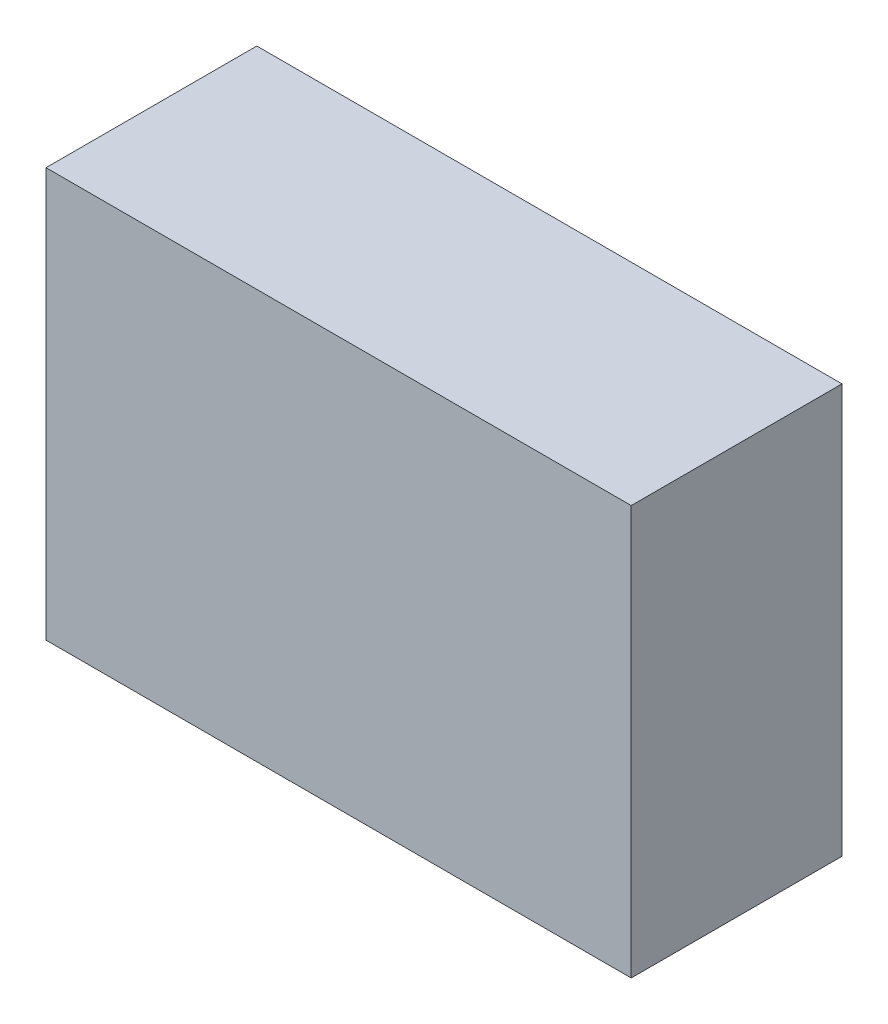
SolidWorks part; units mm, degrees
ref_plane "Front Plane" through (0, 0, 0) normal (0, 0, 1) x (1, 0, 0)
ref_plane "Top Plane" through (0, 0, 0) normal (0, 1, 0) x (1, 0, 0)
ref_plane "Right Plane" through (0, 0, 0) normal (1, 0, 0) x (0, 0, -1)
sketch "Sketch1" plane through (0, 0, 0) normal (0, 0, 1) x (1, 0, 0)
  line L1 (0, 0) -> (59.944, 0)
  line L2 (0, 0) -> (0, 41.91)
  line L3 (0, 41.91) -> (59.944, 41.91)
  line L4 (59.944, 0) -> (59.944, 41.91)
  dimension "D1" = 41.91
  dimension "D2" = 59.944
extrude "Boss-Extrude1" add sketch "Sketch1" along normal blind 21.59
